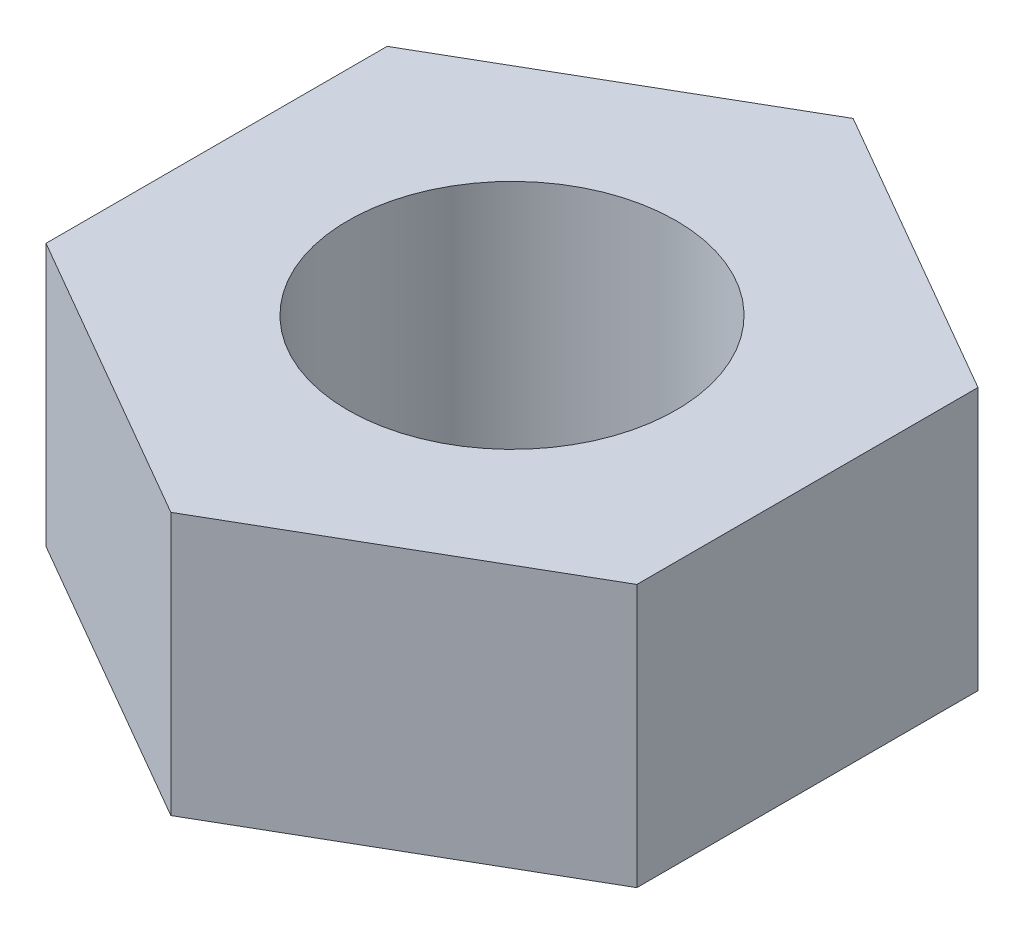
SolidWorks part; units mm, degrees
ref_plane "Front Plane" through (0, 0, 0) normal (0, 0, 1) x (1, 0, 0)
ref_plane "Top Plane" through (0, 0, 0) normal (0, 1, 0) x (1, 0, 0)
ref_plane "Right Plane" through (0, 0, 0) normal (1, 0, 0) x (0, 0, -1)
sketch "Sketch1" plane through (0, 0, 0) normal (0, 1, 0) x (1, 0, 0)
  line L1 (0, 3.1177) -> (-2.7, 1.5588)
  line L2 (-2.7, 1.5588) -> (-2.7, -1.5588)
  line L3 (-2.7, -1.5588) -> (0, -3.1177)
  line L4 (0, -3.1177) -> (2.7, -1.5588)
  line L5 (2.7, -1.5588) -> (2.7, 1.5588)
  line L6 (2.7, 1.5588) -> (0, 3.1177)
  circle A0 centre (0, 0) radius 2.7 construction
extrude "Boss-Extrude1" add sketch "Sketch1" along normal blind 2.4
sketch "Sketch2" plane through (0, 2.4, 0) normal (0, 1, 0) x (1, 0, 0)
  circle A0 centre (0, 0) radius 1.5
extrude "Cut-Extrude1" cut sketch "Sketch2" against normal blind 2.4
